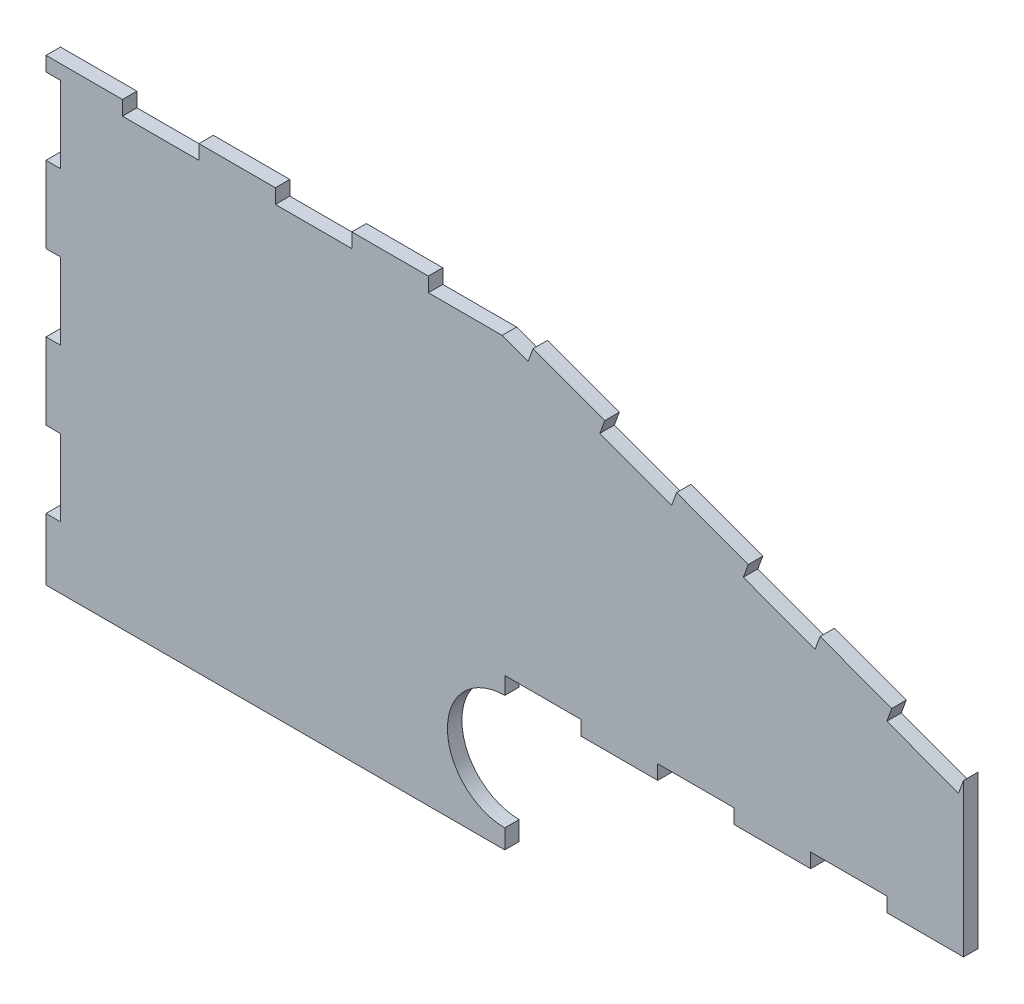
SolidWorks part; units mm, degrees
ref_plane "Front Plane" through (0, 0, 0) normal (0, 0, 1) x (1, 0, 0)
ref_plane "Top Plane" through (0, 0, 0) normal (0, 1, 0) x (1, 0, 0)
ref_plane "Right Plane" through (0, 0, 0) normal (1, 0, 0) x (0, 0, -1)
sketch "Sketch1" plane through (0, 0, 0) normal (0, 0, 1) x (1, 0, 0)
  line L1 (-76.2, -12.7) -> (-76.2, -2.4)
  line L2 (-76.2, 63.5) -> (0, 63.5) construction
  line L3 (4.7063, 61.7645) -> (16.6219, 57.3704)
  line L4 (76.2, 35.4) -> (76.2, 10)
  line L5 (76.2, 10) -> (63.5, 10)
  line L7 (0, 9.525) -> (0, 10)
  line L8 (0, -9.525) -> (0, -12.7)
  line L9 (0, -12.7) -> (-76.2, -12.7)
  line L11 (76.2, 35.4) -> (75.3696, 33.1482)
  line L12 (64.2844, 39.7941) -> (63.454, 37.5423)
  line L13 (75.3696, 33.1482) -> (63.454, 37.5423)
  line L15 (52.3688, 44.1882) -> (51.5384, 41.9364)
  line L16 (40.4531, 48.5822) -> (39.6228, 46.3305)
  line L17 (51.5384, 41.9364) -> (39.6228, 46.3305)
  line L18 (52.3688, 44.1882) -> (64.2844, 39.7941)
  line L19 (28.5375, 52.9763) -> (27.7071, 50.7246)
  line L21 (27.7071, 50.7246) -> (15.7915, 55.1186)
  line L22 (16.6219, 57.3704) -> (15.7915, 55.1186)
  line L24 (4.7063, 61.7645) -> (3.8759, 59.5127)
  line L26 (3.8759, 59.5127) -> (-0.4284, 61.1)
  line L27 (28.5375, 52.9763) -> (40.4531, 48.5822)
  line L28 (0, 63.5) -> (76.2, 35.4) construction
  line L30 (-63.5, 63.5) -> (-63.5, 61.1)
  line L31 (-50.8, 63.5) -> (-50.8, 61.1)
  line L32 (-63.5, 61.1) -> (-50.8, 61.1)
  line L34 (-38.1, 63.5) -> (-38.1, 61.1)
  line L35 (-25.4, 63.5) -> (-25.4, 61.1)
  line L36 (-38.1, 61.1) -> (-25.4, 61.1)
  line L38 (-12.7, 63.5) -> (-12.7, 61.1)
  line L40 (-12.7, 61.1) -> (-0.4284, 61.1)
  line L41 (-12.7, 63.5) -> (-25.4, 63.5)
  line L42 (-63.5, 63.5) -> (-76.2, 63.5)
  line L43 (-50.8, 63.5) -> (-38.1, 63.5)
  line L45 (0, 10) -> (0, 12.4)
  line L46 (12.7, 10) -> (12.7, 12.4)
  line L47 (0, 12.4) -> (12.7, 12.4)
  line L49 (25.4, 10) -> (25.4, 12.4)
  line L50 (38.1, 10) -> (38.1, 12.4)
  line L51 (25.4, 12.4) -> (38.1, 12.4)
  line L53 (50.8, 10) -> (50.8, 12.4)
  line L54 (63.5, 10) -> (63.5, 12.4)
  line L55 (50.8, 12.4) -> (63.5, 12.4)
  line L60 (25.4, 10) -> (12.7, 10)
  line L61 (50.8, 10) -> (38.1, 10)
  line L62 (-76.2, 61.1) -> (-73.8, 61.1)
  line L64 (-73.8, 61.1) -> (-73.8, 48.4)
  line L65 (-76.2, 48.4) -> (-73.8, 48.4)
  line L66 (-76.2, 35.7) -> (-73.8, 35.7)
  line L68 (-73.8, 35.7) -> (-73.8, 23)
  line L69 (-76.2, 23) -> (-73.8, 23)
  line L70 (-76.2, 10.3) -> (-73.8, 10.3)
  line L72 (-73.8, 10.3) -> (-73.8, -2.4)
  line L73 (-76.2, -2.4) -> (-73.8, -2.4)
  line L74 (-76.2, 61.1) -> (-76.2, 63.5)
  line L75 (-76.2, 35.7) -> (-76.2, 48.4)
  line L76 (-76.2, 10.3) -> (-76.2, 23)
  arc A1 (0, 9.525) -> (0, -9.525) centre (0, 0) ccw
  point P26 (25.4, 12.4)
  point P57 (0, 0)
  dimension "D1" = 10
  dimension "D3" = 3.175
  dimension "D2" = 19.05
  dimension "D4" = 25.4
  dimension "D5" = 76.2
  dimension "D6" = 76.2
  dimension "D7" = 2.4
  dimension "D8" = 76.2
  dimension "D9" = 2.4
  dimension "D10" = 12.7
  dimension "D11" = 12.7
  dimension "D12" = 12.7
  dimension ".5" = 12.7
  dimension "D13" = 12.7
  dimension "D14" = 12.7
  dimension "D15" = 2.4
  dimension "D16" = 2.4
  dimension "D17" = 12.7
  dimension "D18" = 12.7
  dimension "D19" = 12.7
  dimension "D20" = 12.7
  dimension "D21" = 12.7
  dimension "D22" = 12.7
  dimension "D23" = 12.7
  dimension "D24" = 12.7
  dimension "D25" = 12.7
  dimension "D26" = 12.7
  dimension "D27" = 12.7
  dimension "D28" = 12.7
  dimension "D29" = 12.7
  dimension "D30" = 12.7
  dimension "D31" = 12.7
  dimension "D32" = 12.7
  dimension "D33" = 2.4
  dimension "D34" = 2.4
  dimension "D35" = 2.4
extrude "Boss-Extrude1" add sketch "Sketch1" along normal blind 2.4
